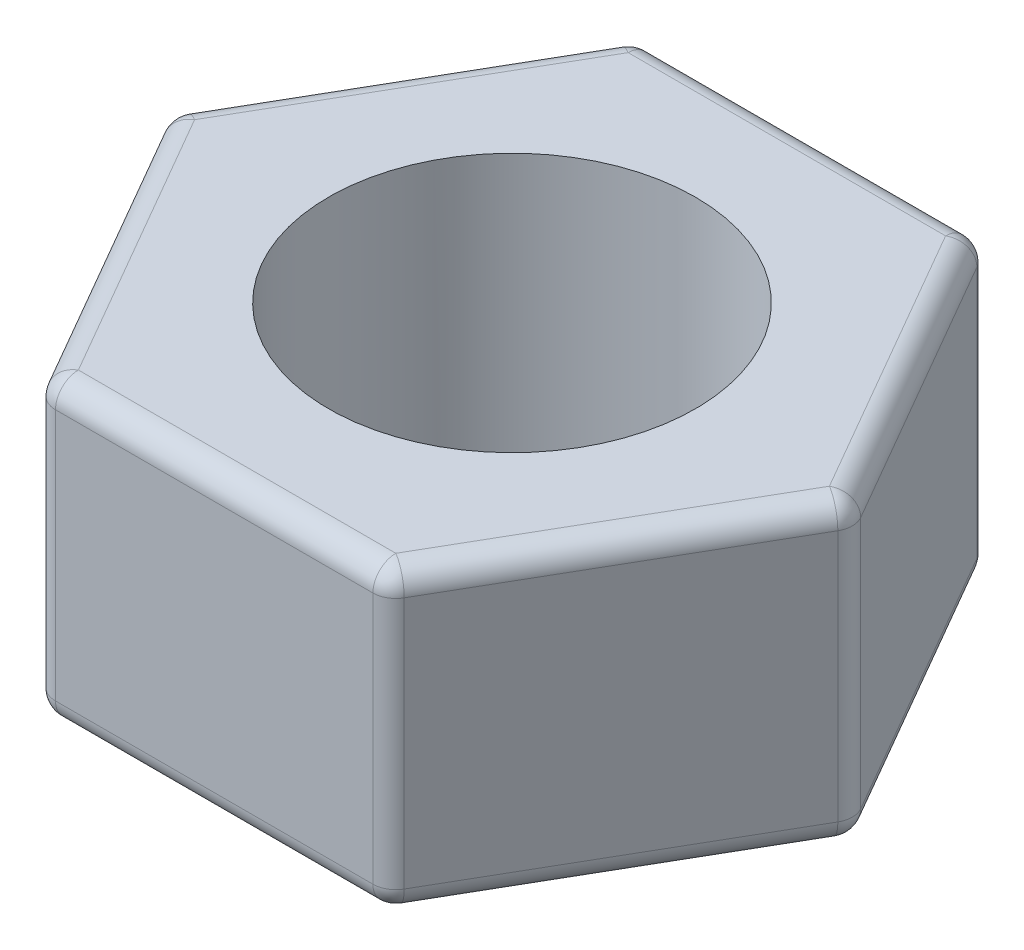
SolidWorks part; units mm, degrees
ref_plane "Front Plane" through (0, 0, 0) normal (0, 0, 1) x (1, 0, 0)
ref_plane "Top Plane" through (0, 0, 0) normal (0, 1, 0) x (1, 0, 0)
ref_plane "Right Plane" through (0, 0, 0) normal (1, 0, 0) x (0, 0, -1)
sketch "Sketch1" plane through (0, 0, 0) normal (0, 1, 0) x (1, 0, 0)
  line L1 (7.5, 0) -> (3.75, 6.4952)
  line L2 (3.75, 6.4952) -> (-3.75, 6.4952)
  line L3 (-3.75, 6.4952) -> (-7.5, 0)
  line L4 (-7.5, 0) -> (-3.75, -6.4952)
  line L5 (-3.75, -6.4952) -> (3.75, -6.4952)
  line L6 (3.75, -6.4952) -> (7.5, 0)
  circle A1 centre (0, 0) radius 7.5 construction
extrude "Extrude3" add sketch "Sketch1" along normal blind 6.5
fillet "Fillet3" radius 0.5 18 edges at (0, 6.5, 6.4952) (-5.625, 6.5, 3.2476) (-3.75, 3.25, 6.4952) (-5.625, 6.5, -3.2476) (-7.5, 3.25, 0) (0, 6.5, -6.4952) (-3.75, 3.25, -6.4952) (3.75, 3.25, 6.4952) (5.625, 6.5, 3.2476) (0, 0, -6.4952) (-5.625, 0, -3.2476) (-5.625, 0, 3.2476) (0, 0, 6.4952) (5.625, 0, 3.2476) (7.5, 3.25, 0) (5.625, 6.5, -3.2476) (3.75, 3.25, -6.4952) (5.625, 0, -3.2476)
sketch "Sketch2" plane through (0, 0, 0) normal (0, -1, 0) x (1, 0, 0)
  circle A0 centre (0, 0) radius 4
extrude "Extrude4" cut sketch "Sketch2" against normal blind 6.5
fillet "Fillet5" radius 0.5 1 edges at (0, 0, -4)
